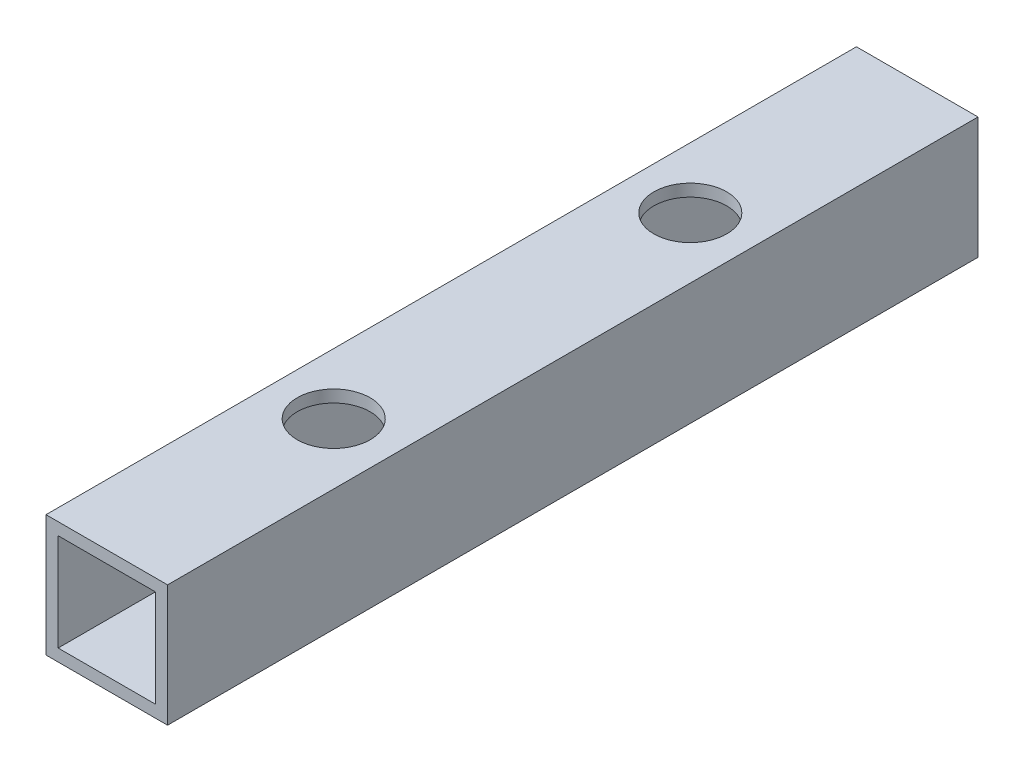
SolidWorks part; units mm, degrees
ref_plane "正面" through (0, 0, 0) normal (0, 0, 1) x (1, 0, 0)
ref_plane "平面" through (0, 0, 0) normal (0, 1, 0) x (1, 0, 0)
ref_plane "右側面" through (0, 0, 0) normal (1, 0, 0) x (0, 0, -1)
sketch "ｽｹｯﾁ1" plane through (0, 0, 0) normal (0, 0, 1) x (1, 0, 0)
  line L1 (-6, 6) -> (6, 6)
  line L2 (-6, 6) -> (-6, -6)
  line L3 (-6, -6) -> (6, -6)
  line L4 (6, 6) -> (6, -6)
  line L5 (-6, 6) -> (6, -6) construction
  line L6 (-6, -6) -> (6, 6) construction
  line L7 (-7.5, 7.5) -> (7.5, 7.5)
  line L8 (-7.5, 7.5) -> (-7.5, -7.5)
  line L9 (-7.5, -7.5) -> (7.5, -7.5)
  line L10 (7.5, 7.5) -> (7.5, -7.5)
  line L11 (-7.5, 7.5) -> (7.5, -7.5) construction
  line L12 (-7.5, -7.5) -> (7.5, 7.5) construction
  point P1 (0, 0)
  point P6 (0, 0)
  dimension "D1" = 12
  dimension "D2" = 12
  dimension "D3" = 15
  dimension "D4" = 15
extrude "ﾎﾞｽ - 押し出し1" add sketch "ｽｹｯﾁ1" along normal blind 100
sketch "ｽｹｯﾁ2" plane through (0, 7.5, 0) normal (0, 1, 0) x (1, 0, 0)
  line L0 (7.5, -50) -> (0, -50)
  line L1 (7.5, -100) -> (7.5, 0) construction
  line L2 (0, -50) -> (0, -28)
  line L3 (0, -50) -> (0, -72)
  circle A0 centre (0, -72) radius 4.5
  circle A1 centre (0, -28) radius 4.5
  dimension "D4" = 9
  dimension "D5" = 9
  dimension "D1" = 7.5
  dimension "D2" = 22
  dimension "D3" = 22
extrude "ｶｯﾄ - 押し出し1" cut sketch "ｽｹｯﾁ2" against normal blind 60
